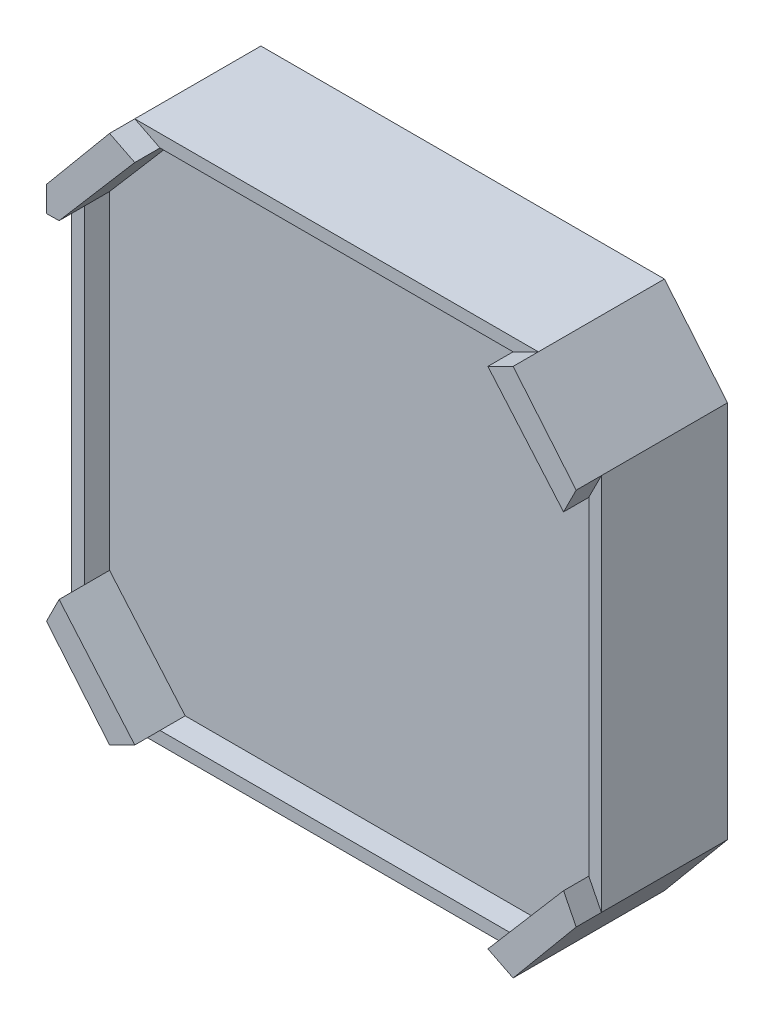
SolidWorks part; units mm, degrees
ref_plane "Alzado" through (0, 0, 0) normal (0, 0, 1) x (1, 0, 0)
ref_plane "Planta" through (0, 0, 0) normal (0, 1, 0) x (1, 0, 0)
ref_plane "Vista lateral" through (0, 0, 0) normal (1, 0, 0) x (0, 0, -1)
sketch "Croquis2" plane through (0, 0, 0) normal (0, 0, 1) x (1, 0, 0)
  line L0 (0, 21) -> (0, 32.1176) construction
  line L1 (-16, 21) -> (16, 21)
  line L2 (-21, 15) -> (-21, -15)
  line L3 (-16, -21) -> (16, -21)
  line L4 (21, 15) -> (21, -15)
  line L5 (-21, 21) -> (21, -21) construction
  line L6 (-21, -21) -> (21, 21) construction
  line L7 (0, 32.1176) -> (-16, 32.1176) construction
  line L8 (-16, 21) -> (-16, 15) construction
  line L9 (-16, 21) -> (-21, 15)
  line L10 (16, 21) -> (21, 15)
  line L11 (0, 0) -> (3.8385, 0) construction
  line L12 (16, -21) -> (21, -15)
  line L13 (-16, -21) -> (-21, -15)
  point P0 (0, 0)
  dimension "D1" = 42
  dimension "D2" = 42
extrude "Saliente-Extruir1" add sketch "Croquis2" along normal blind 10
sketch "Croquis3" plane through (0, 0, 10) normal (0, 0, 1) x (1, 0, 0)
  line L0 (-20, 8.0237) -> (-14, 8.0237) construction
  line L1 (-14, 20) -> (14, 20)
  line L2 (-20, 13.0049) -> (-20, -13.0049)
  line L3 (-14, -20) -> (14, -20)
  line L4 (20, 13.0049) -> (20, -13.0049)
  line L5 (-20, 20) -> (20, -20) construction
  line L6 (-20, -20) -> (20, 20) construction
  line L7 (-14, 20) -> (-14, 14) construction
  line L8 (-14, 20) -> (-20, 13.0049)
  line L9 (0, 0) -> (0, 5.1257) construction
  line L10 (0, 0) -> (6.8139, 0) construction
  line L11 (14, 20) -> (20, 13.0049)
  line L12 (14, -20) -> (20, -13.0049)
  line L13 (-14, -20) -> (-20, -13.0049)
  point P0 (0, 0)
  dimension "D1" = 40
  dimension "D2" = 40
extrude "Cortar-Extruir1" cut sketch "Croquis3" against normal blind 2
sketch "Croquis4" plane through (0, 0, 10) normal (0, 0, 1) x (1, 0, 0)
  line L0 (-16, 21) -> (-21, 15)
  line L1 (-21, 15) -> (-21, 12.992)
  line L2 (-21, 15) -> (-21, -15) construction
  line L3 (-21, 12.992) -> (-20, 13.0049)
  line L4 (-20, 13.0049) -> (-14, 20)
  line L5 (-14, 20) -> (-16, 21)
  line L6 (16, 21) -> (21, 15)
  line L7 (21, 15) -> (20, 13.0049)
  line L8 (20, 13.0049) -> (14, 20)
  line L9 (14, 20) -> (16, 21)
  line L10 (16, 21) -> (16.1281, 21.0712)
  line L11 (20, -13.0049) -> (14, -20)
  line L12 (14, -20) -> (16, -21)
  line L13 (16, -21) -> (21, -15)
  line L14 (21, -15) -> (20, -13.0049)
  line L15 (-14, -20) -> (-20, -13.0049)
  line L16 (-20, -13.0049) -> (-21, -15)
  line L17 (-21, -15) -> (-16, -21)
  line L18 (-16, -21) -> (-14, -20)
  line M8 (-14, -20) -> (-20, -13.0049)
  line M11 (-21, -15) -> (-16, -21)
extrude "Saliente-Extruir2" add sketch "Croquis4" along normal blind 2 contours L18 L16 M11 M8 | L4 L5 L0 L1 L3 | L6 L7 L8 L9 | L13 L14 L11 L12
sketch "Croquis5" plane through (0, -21, 0) normal (0, -1, 0) x (1, 0, 0)
  line L0 (0, 0) -> (0, 10) construction
  line L1 (-16, 10) -> (16, 10) construction
  line L3 (-2, 6.5) -> (2, 6.5)
  line L4 (-2, 6.5) -> (-2, 3.5)
  line L5 (-2, 3.5) -> (2, 3.5)
  line L6 (2, 6.5) -> (2, 3.5)
  line L7 (-2, 6.5) -> (2, 3.5) construction
  line L8 (-2, 3.5) -> (2, 6.5) construction
  point P5 (0, 5)
  dimension "D1" = 4
  dimension "D2" = 3
extrude "Cortar-Extruir2" cut sketch "Croquis5" against normal blind 3
sketch "Croquis6" plane through (0, 0, 0) normal (0, 0, -1) x (-1, 0, 0)
  line L0 (0, 0) -> (15.5, 0) construction
  line L1 (0, 0) -> (0, 4.535) construction
  line L2 (15.5, 0) -> (15.5, 15.5) construction
  circle A0 centre (15.5, 15.5) radius 1.4
  circle A1 centre (-15.5, 15.5) radius 1.4
  circle A2 centre (15.5, -15.5) radius 1.4
  circle A3 centre (-15.5, -15.5) radius 1.4
  dimension "D2" = 2.8
  dimension "D1" = 15.5
extrude "Cortar-Extruir3" cut sketch "Croquis6" against normal blind 5
